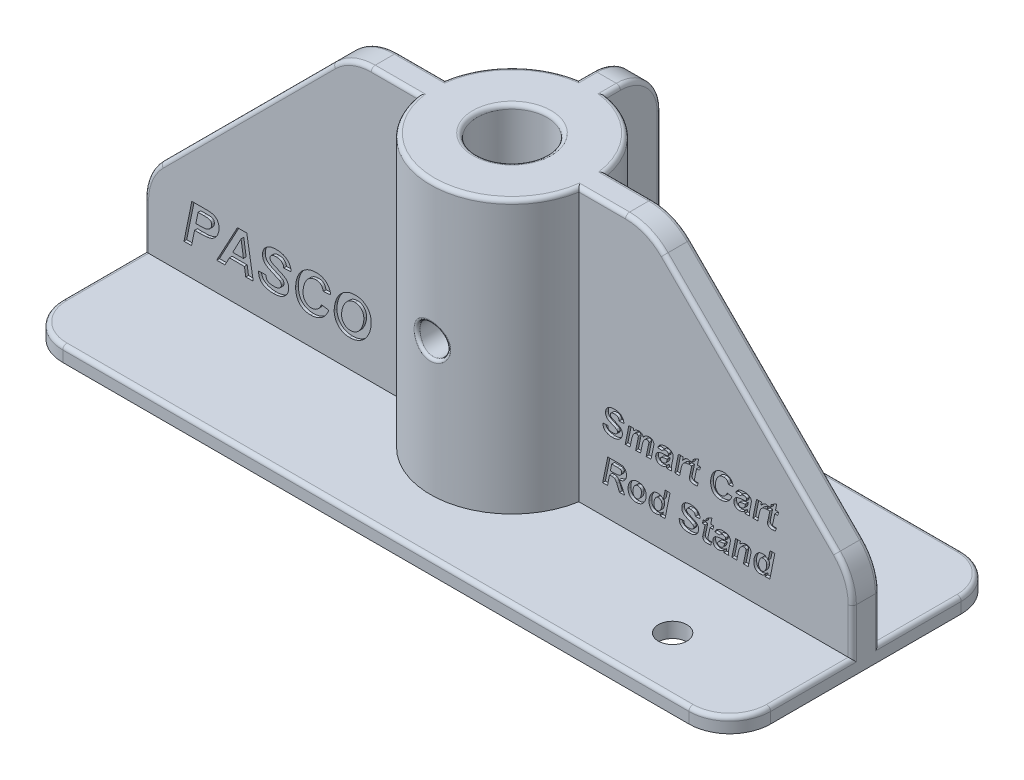
SolidWorks part; units mm, degrees
ref_plane "Front Plane" through (0, 0, 0) normal (0, 0, 1) x (1, 0, 0)
ref_plane "Top Plane" through (0, 0, 0) normal (0, 1, 0) x (1, 0, 0)
ref_plane "Right Plane" through (0, 0, 0) normal (1, 0, 0) x (0, 0, -1)
sketch "Sketch1 Base" plane through (0, 0, 0) normal (0, 1, 0) x (1, 0, 0)
  line L1 (-66.04, 25.4) -> (66.04, 25.4)
  line L2 (-66.04, 25.4) -> (-66.04, -25.4)
  line L3 (-66.04, -25.4) -> (66.04, -25.4)
  line L4 (66.04, 25.4) -> (66.04, -25.4)
  line L5 (-66.04, 25.4) -> (66.04, -25.4) construction
  line L6 (-66.04, -25.4) -> (66.04, 25.4) construction
  circle A0 centre (-44.958, 14.986) radius 2.667
  circle A1 centre (44.958, -14.986) radius 2.667
  point P0 (0, 0)
  dimension "D5" = 5.334
  dimension "D6" = 5.334
  dimension "D1" = 50.8
  dimension "D2" = 132.08
  dimension "D3" = 21.082
  dimension "D4" = 10.414
  dimension "D7" = 21.082
  dimension "D8" = 10.414
extrude "Boss-Extrude1" add sketch "Sketch1 Base" along normal blind 2.794
sketch "Sketch1" plane through (0, 2.794, 0) normal (0, 1, 0) x (1, 0, 0)
  line L0 (-66.04, 25.4) -> (-66.04, -25.4) construction
  line L1 (-66.04, -2.54) -> (66.04, -2.54)
  line L2 (-66.04, -2.54) -> (-66.04, 2.54)
  line L3 (-66.04, 2.54) -> (66.04, 2.54)
  line L4 (66.04, -2.54) -> (66.04, 2.54)
  line L5 (-66.04, -2.54) -> (66.04, 2.54) construction
  line L6 (-66.04, 2.54) -> (66.04, -2.54) construction
  point P0 (0, 0)
  dimension "D1" = 5.08
extrude "Boss-Extrude2" add sketch "Sketch1" along normal blind 50.8
sketch "Sketch2" plane through (0, 2.794, 0) normal (0, 1, 0) x (1, 0, 0)
  line L0 (66.04, 25.4) -> (-66.04, 25.4) construction
  line L1 (2.4419, 0.6125) -> (-2.6381, 0.6125)
  line L2 (2.4419, 0.6125) -> (2.4419, 25.4)
  line L3 (2.4419, 25.4) -> (-2.6381, 25.4)
  line L4 (-2.6381, 0.6125) -> (-2.6381, 25.4)
  line L5 (2.4419, 0.6125) -> (-2.6381, 25.4) construction
  line L6 (2.4419, 25.4) -> (-2.6381, 0.6125) construction
  point P0 (-0.0981, 13.0063)
  dimension "D1" = 5.08
extrude "Boss-Extrude3" add sketch "Sketch2" along normal blind 50.8
sketch "Sketch3" plane through (0, 2.794, 0) normal (0, 1, 0) x (1, 0, 0)
  circle A0 centre (0, 0) radius 15.24
  dimension "D1" = 30.48
extrude "Boss-Extrude4" add sketch "Sketch3" along normal blind 50.8
sketch "Sketch4" plane through (0, 53.594, 0) normal (0, 1, 0) x (1, 0, 0)
  circle A0 centre (0, 0) radius 6.5405
  dimension "D1" = 13.081
extrude "Cut-Extrude1" cut sketch "Sketch4" against normal through all
sketch "Sketch6" plane through (0, 0, 0) normal (0, 0, 1) x (1, 0, 0)
  circle A0 centre (0, 27.6562) radius 2.794
  dimension "D1" = 5.588
extrude "Cut-Extrude3" cut sketch "Sketch6" along normal blind 38.862
chamfer "Chamfer1" distance 38.1 angle 45 2 edges at (66.04, 53.594, 0) (-66.04, 53.594, 0)
fillet "Fillet6" radius 10.16 4 edges at (-66.04, 15.494, 0) (66.04, 15.494, 0) (27.94, 53.594, 0) (-27.94, 53.594, 0)
fillet "Fillet7" radius 7.62 1 edges at (-0.0981, 53.594, -25.4)
fillet "Fillet8" radius 7.62 4 edges at (-66.04, 1.397, 25.4) (-66.04, 1.397, -25.4) (66.04, 1.397, -25.4) (66.04, 1.397, 25.4)
sketch "Sketch7" plane through (0, 0, 2.54) normal (0, 0, 1) x (1, 0, 0)
  text T0 "PASCO" font "Arial" height in points 28
extrude "Cut-Extrude4" cut sketch "Sketch7" against normal blind 0.508
sketch "Sketch8" plane through (0, 0, 2.54) normal (0, 0, 1) x (1, 0, 0)
  text T0 "Smart Cart\r\nRod Stand" font "Arial" height in points 18
extrude "Cut-Extrude5" cut sketch "Sketch8" against normal blind 0.508
fillet "Fillet9" radius 0.762 26 edges at (19.3792, 53.594, -2.54) (27.6197, 52.8206, -2.54) (66.04, 7.0398, -2.54) (65.2666, 15.1737, -2.54) (66.04, 7.0398, 2.54) (65.2666, 15.1737, 2.54) (19.3792, 53.594, 2.54) (27.6197, 52.8206, 2.54) (-19.3792, 53.594, 2.54) (-27.6197, 52.8206, 2.54) (-66.04, 7.0398, 2.54) (-65.2666, 15.1737, 2.54) (30.431, 2.794, -25.4) (63.8082, 2.794, -23.1682) (-66.04, 2.794, 10.16) (-63.8082, 2.794, 23.1682) (66.04, 2.794, 10.16) (63.8082, 2.794, 23.1682) (46.99, 34.544, -2.54) (46.99, 34.544, 2.54) (-46.99, 34.544, 2.54) (66.04, 2.794, -10.16) (0, 2.794, 25.4) (2.4419, 53.594, -16.4115) (2.4419, 51.3622, -23.1682) (2.4419, 24.384, -25.4)
fillet "Fillet10" radius 0.762 11 edges at (-66.04, 2.794, -10.16) (-63.8082, 2.794, -23.1682) (-30.529, 2.794, -25.4) (-2.6381, 53.594, -16.395) (-2.6381, 51.3622, -23.1682) (-66.04, 7.0398, -2.54) (-65.2666, 15.1737, -2.54) (-19.3792, 53.594, -2.54) (-27.6197, 52.8206, -2.54) (-2.6381, 24.384, -25.4) (-46.99, 34.544, -2.54)
fillet "Fillet11" radius 0.762 3 edges at (10.7414, 53.594, -10.8111) (-10.8112, 53.594, -10.7413) (0, 53.594, 15.24)
fillet "Fillet12" radius 0.508 1 edges at (0.3738, 30.4251, 6.5298)
fillet "Fillet13" radius 0.508 1 edges at (2.7309, 28.2467, 14.9933)
fillet "Fillet14" radius 0.762 1 edges at (0, 53.594, 6.5405)
